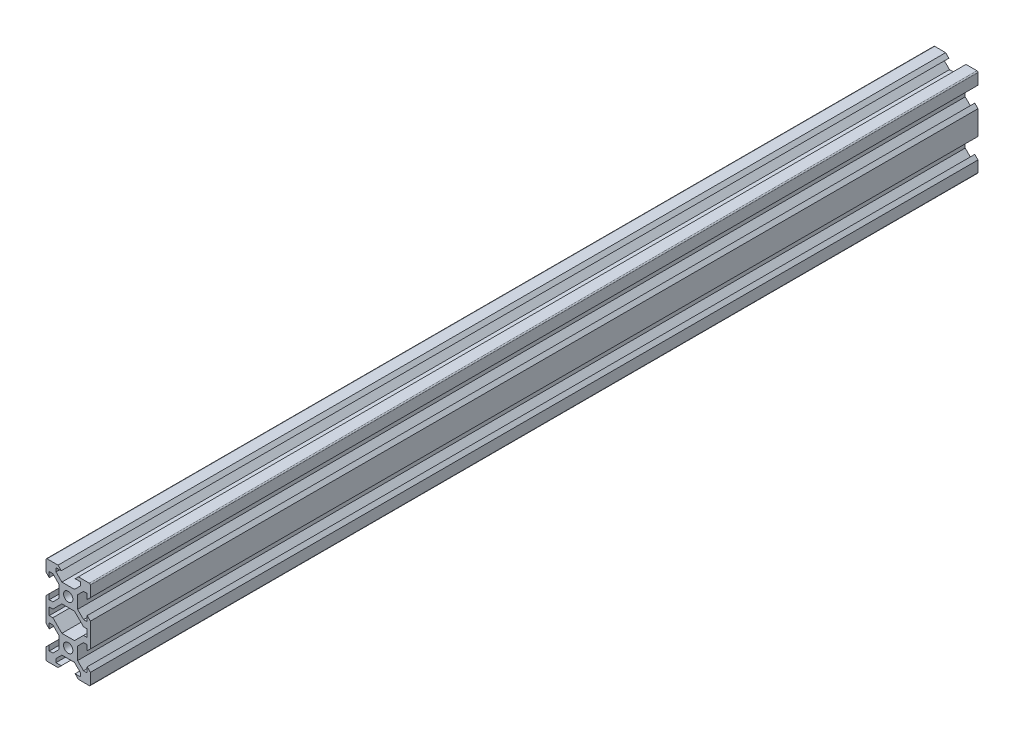
SolidWorks part; units mm, degrees
ref_plane "Front Plane" through (0, 0, 0) normal (0, 0, 1) x (1, 0, 0)
ref_plane "Top Plane" through (0, 0, 0) normal (0, 1, 0) x (1, 0, 0)
ref_plane "Right Plane" through (0, 0, 0) normal (1, 0, 0) x (0, 0, -1)
sketch "Sketch2" plane through (0, 0, 0) normal (0, 0, 1) x (1, 0, 0)
  line L0 (-4.58, -10) -> (-3.125, -8.545)
  line L1 (-9.5, -10) -> (9.5, -10)
  line L2 (-10, -9.5) -> (-10, 29.5)
  line L3 (-10, 10) -> (10, 10)
  line L4 (10, -9.5) -> (10, 29.5)
  line L5 (-10, -10) -> (10, 10) construction
  line L6 (-10, 10) -> (10, -10) construction
  line L7 (-3.125, -8.545) -> (-5.5, -8.545)
  line L8 (0, 4.8178) -> (0, -5.9385) construction
  line L9 (-8.545, 3.125) -> (-10, 4.58)
  line L10 (-8.545, 5.5) -> (-8.545, 3.125)
  line L11 (5.5, -8.545) -> (3.125, -8.545)
  line L12 (3.125, -8.545) -> (4.58, -10)
  line L13 (-3.125, -8.545) -> (3.125, -8.545) construction
  line L14 (-5.5, -8.545) -> (-5.5, -6.905)
  line L15 (-5.5, -6.905) -> (-2.84, -4.245)
  line L16 (-2.84, -4.245) -> (2.84, -4.245)
  line L17 (2.84, -4.245) -> (5.5, -6.905)
  line L18 (5.5, -6.905) -> (5.5, -8.545)
  line L19 (-6.905, 5.5) -> (-8.545, 5.5)
  line L20 (-4.245, 2.84) -> (-6.905, 5.5)
  line L21 (-10, -4.58) -> (-8.545, -3.125)
  line L22 (-8.545, -3.125) -> (-8.545, -5.5)
  line L23 (-8.545, -5.5) -> (-6.905, -5.5)
  line L24 (-6.905, -5.5) -> (-4.245, -2.84)
  line L25 (-4.245, -2.84) -> (-4.245, 2.84)
  line L26 (10, -4.58) -> (8.545, -3.125)
  line L27 (8.545, -3.125) -> (8.545, -5.5)
  line L28 (8.545, -5.5) -> (6.905, -5.5)
  line L29 (6.905, -5.5) -> (4.245, -2.84)
  line L30 (4.245, -2.84) -> (4.245, 2.84)
  line L31 (4.245, 2.84) -> (6.905, 5.5)
  line L32 (6.905, 5.5) -> (8.545, 5.5)
  line L33 (8.545, 3.125) -> (10, 4.58)
  line L34 (8.545, 5.5) -> (8.545, 3.125)
  line L35 (-3.7027, 0) -> (5.6465, 0) construction
  line L36 (-2.84, 4.245) -> (2.84, 4.245)
  line L37 (-2.84, 4.245) -> (-6.905, 8.31)
  line L38 (-6.905, 8.31) -> (-8.545, 8.31)
  line L39 (-8.545, 8.31) -> (-8.545, 11.69)
  line L40 (-8.545, 10) -> (8.545, 10)
  line L41 (8.545, 11.69) -> (8.545, 8.31)
  line L42 (8.545, 8.31) -> (6.905, 8.31)
  line L43 (6.905, 8.31) -> (2.84, 4.245)
  line L44 (-10, 4.58) -> (-10, -4.58)
  line L45 (10, 4.58) -> (10, -4.58)
  line L46 (-4.58, -10) -> (4.58, -10)
  line L47 (-3.7027, 20) -> (5.6465, 20) construction
  line L48 (-3.125, 28.545) -> (3.125, 28.545) construction
  line L49 (0, 15.1822) -> (0, 25.9385) construction
  line L50 (-10, 10) -> (10, 30) construction
  line L51 (-10, 30) -> (10, 10) construction
  line L52 (-4.58, 30) -> (4.58, 30)
  line L53 (10, 15.42) -> (10, 24.58)
  line L54 (-10, 15.42) -> (-10, 24.58)
  line L55 (6.905, 11.69) -> (2.84, 15.755)
  line L56 (8.545, 11.69) -> (6.905, 11.69)
  line L57 (-6.905, 11.69) -> (-8.545, 11.69)
  line L58 (-2.84, 15.755) -> (-6.905, 11.69)
  line L59 (-2.84, 15.755) -> (2.84, 15.755)
  line L60 (8.545, 14.5) -> (8.545, 16.875)
  line L61 (8.545, 16.875) -> (10, 15.42)
  line L62 (6.905, 14.5) -> (8.545, 14.5)
  line L63 (4.245, 17.16) -> (6.905, 14.5)
  line L64 (4.245, 22.84) -> (4.245, 17.16)
  line L65 (6.905, 25.5) -> (4.245, 22.84)
  line L66 (8.545, 25.5) -> (6.905, 25.5)
  line L67 (8.545, 23.125) -> (8.545, 25.5)
  line L68 (10, 24.58) -> (8.545, 23.125)
  line L69 (-4.245, 22.84) -> (-4.245, 17.16)
  line L70 (-6.905, 25.5) -> (-4.245, 22.84)
  line L71 (-8.545, 25.5) -> (-6.905, 25.5)
  line L72 (-8.545, 23.125) -> (-8.545, 25.5)
  line L73 (-10, 24.58) -> (-8.545, 23.125)
  line L74 (-4.245, 17.16) -> (-6.905, 14.5)
  line L75 (-6.905, 14.5) -> (-8.545, 14.5)
  line L76 (5.5, 26.905) -> (5.5, 28.545)
  line L77 (2.84, 24.245) -> (5.5, 26.905)
  line L78 (-2.84, 24.245) -> (2.84, 24.245)
  line L79 (-5.5, 26.905) -> (-2.84, 24.245)
  line L80 (-5.5, 28.545) -> (-5.5, 26.905)
  line L81 (3.125, 28.545) -> (4.58, 30)
  line L82 (5.5, 28.545) -> (3.125, 28.545)
  line L83 (-8.545, 14.5) -> (-8.545, 16.875)
  line L84 (-8.545, 16.875) -> (-10, 15.42)
  line L85 (-3.125, 28.545) -> (-5.5, 28.545)
  line L86 (-9.5, 30) -> (9.5, 30)
  line L87 (-4.58, 30) -> (-3.125, 28.545)
  circle A0 centre (0, 0) radius 2.1
  arc A1 (9.5, -10) -> (10, -9.5) centre (9.5, -9.5) ccw
  arc A2 (-9.5, -10) -> (-10, -9.5) centre (-9.5, -9.5) cw
  arc A3 (-9.5, 30) -> (-10, 29.5) centre (-9.5, 29.5) ccw
  arc A4 (9.5, 30) -> (10, 29.5) centre (9.5, 29.5) cw
  circle A5 centre (0, 20) radius 2.1
  point P15 (0, -8.545)
  point P18 (0, -4.245)
  dimension "D1" = 4.2
  dimension "D4" = 0.5
  dimension "D2" = 20
  dimension "D3" = 20
  dimension "D5" = 6.25
  dimension "D6" = 5.68
  dimension "D7" = 11
  dimension "D8" = 9.16
  dimension "D9" = 135
  dimension "D10" = 4.3
  dimension "D11" = 45
  dimension "D12" = 4.58
  dimension "D13" = 135
  dimension "D14" = 1.64
  dimension "D15" = 1.69
  dimension "D16" = 1.64
  dimension "D17" = 1.69
extrude "Boss-Extrude1" add sketch "Sketch2" along normal blind 400 contours A4 L86 L81 L82 L76 L77 L78 L79 L80 L85 L87 A3 L2 L73 L72 L71 L70 L69 L74 L75 L83 L84 L3 L39 L57 L58 L59 L55 L56 L41 L4 L61 L60 L62 L63 L64 L65 L66 L67 L68 A5 | A2 L1 L0 L7 L14 L15 L16 L17 L18 L11 L12 A1 L4 L26 L27 L28 L29 L30 L31 L32 L34 L33 L3 L41 L42 L43 L36 L37 L38 L39 L2 L9 L10 L19 L20 L25 L24 L23 L22 L21 A0
